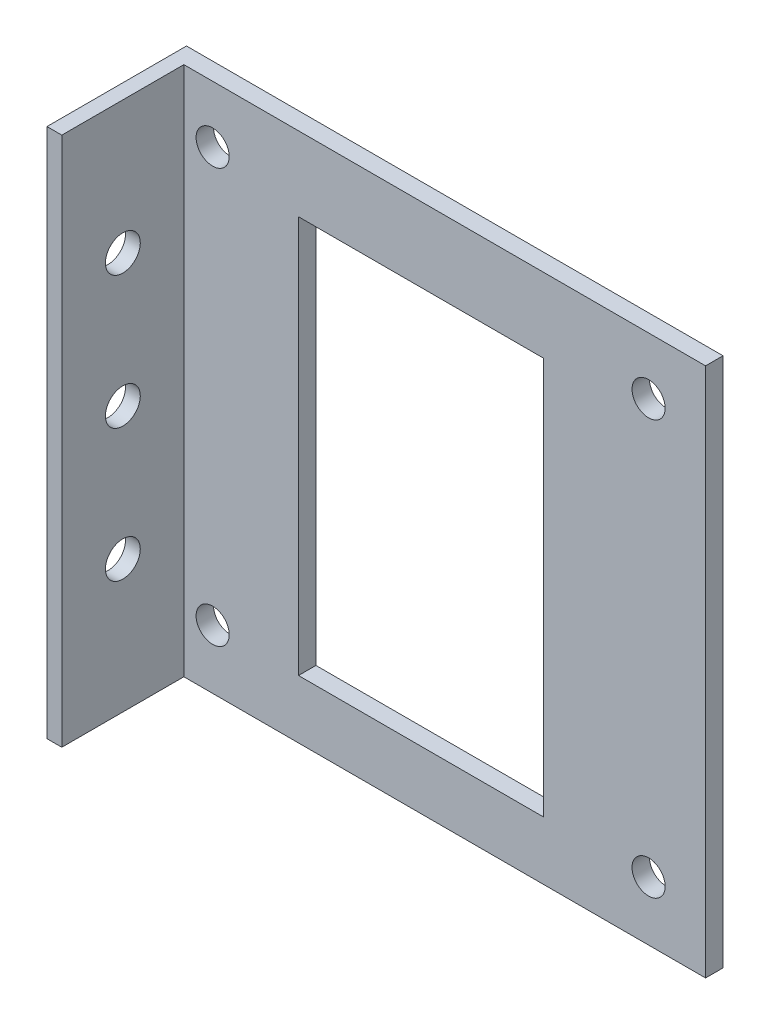
SolidWorks part; units mm, degrees
material "6061-T6 (SS)"
ref_plane "Front Plane" through (0, 0, 0) normal (0, 0, 1) x (1, 0, 0)
ref_plane "Top Plane" through (0, 0, 0) normal (0, 1, 0) x (1, 0, 0)
ref_plane "Right Plane" through (0, 0, 0) normal (1, 0, 0) x (0, 0, -1)
sketch "Sketch2" plane through (0, 0, 0) normal (0, 0, 1) x (1, 0, 0)
  line L25 (-32.5877, 30.9741) -> (45.5627, 30.9741)
  line L26 (-32.5877, 30.9741) -> (-32.5877, -46.2479)
  line L27 (-32.5877, -46.2479) -> (45.5627, -46.2479)
  line L28 (45.5627, 30.9741) -> (45.5627, -46.2479)
  line L29 (21.9185, -37.7384) -> (-13.7342, -37.7384)
  line L30 (21.9185, -37.7384) -> (21.9185, 20.1359)
  line L31 (21.9185, 20.1359) -> (-13.7342, 20.1359)
  line L32 (-13.7342, -37.7384) -> (-13.7342, 20.1359)
  circle A10 centre (-26.2377, 22.6765) radius 2.413
  circle A11 centre (37.2623, 22.6765) radius 2.413
  circle A12 centre (37.2623, -37.6485) radius 2.413
  circle A13 centre (-26.2377, -37.6485) radius 2.413
  dimension "D1" = 4.826
  dimension "D2" = 21.9185
  dimension "D3" = 37.2623
  dimension "D4" = 45.5627
  dimension "D5" = 13.7342
  dimension "D6" = 26.2377
  dimension "D7" = 32.5877
  dimension "D8" = 20.1359
  dimension "D9" = 22.6765
  dimension "D10" = 30.9741
  dimension "D11" = 37.6485
  dimension "D12" = 37.7384
  dimension "D13" = 46.2479
extrude "Boss-Extrude1" add sketch "Sketch2" along normal blind 2.54
sketch "Sketch3" plane through (0, 0, 2.54) normal (0, 0, 1) x (1, 0, 0)
  line L0 (-32.5877, -46.2479) -> (45.5627, -46.2479) construction
  line L5 (45.5627, -46.2479) -> (45.5627, 30.9741) construction
  line L10 (-32.5877, 30.9741) -> (-30.4281, 30.9741)
  line L11 (-32.5877, 30.9741) -> (-32.5877, -46.2479)
  line L12 (-32.5877, -46.2479) -> (-30.4281, -46.2479)
  line L13 (-30.4281, 30.9741) -> (-30.4281, -46.2479)
  line L14 (45.5627, 30.9741) -> (-32.5877, 30.9741) construction
  dimension "D1" = 75.9909
extrude "Boss-Extrude2" add sketch "Sketch3" along normal blind 17.78
sketch "Sketch5" plane through (-30.4281, 0, 0) normal (1, 0, 0) x (0, 0, -1)
  line L0 (-11.43, -46.2479) -> (-11.43, 30.9741) construction
  line L3 (-20.32, -46.2479) -> (-2.54, -46.2479) construction
  line L5 (-20.32, 30.9741) -> (-2.54, 30.9741) construction
  line L6 (-11.43, -7.6369) -> (-2.54, -7.6369) construction
  line L7 (-2.54, -46.2479) -> (-2.54, 30.9741) construction
  line L8 (-6.985, -7.6369) -> (-6.985, 30.9741) construction
  line L9 (-6.985, 11.6686) -> (-11.43, 11.6686) construction
  circle A4 centre (-11.43, -7.6369) radius 2.54
  circle A5 centre (-11.43, 11.6686) radius 2.54
  circle A6 centre (-11.43, -26.9424) radius 2.54
  dimension "D1" = 5.08
  dimension "D2" = 5.08
extrude "Cut-Extrude2" cut sketch "Sketch5" against normal blind 17.78
